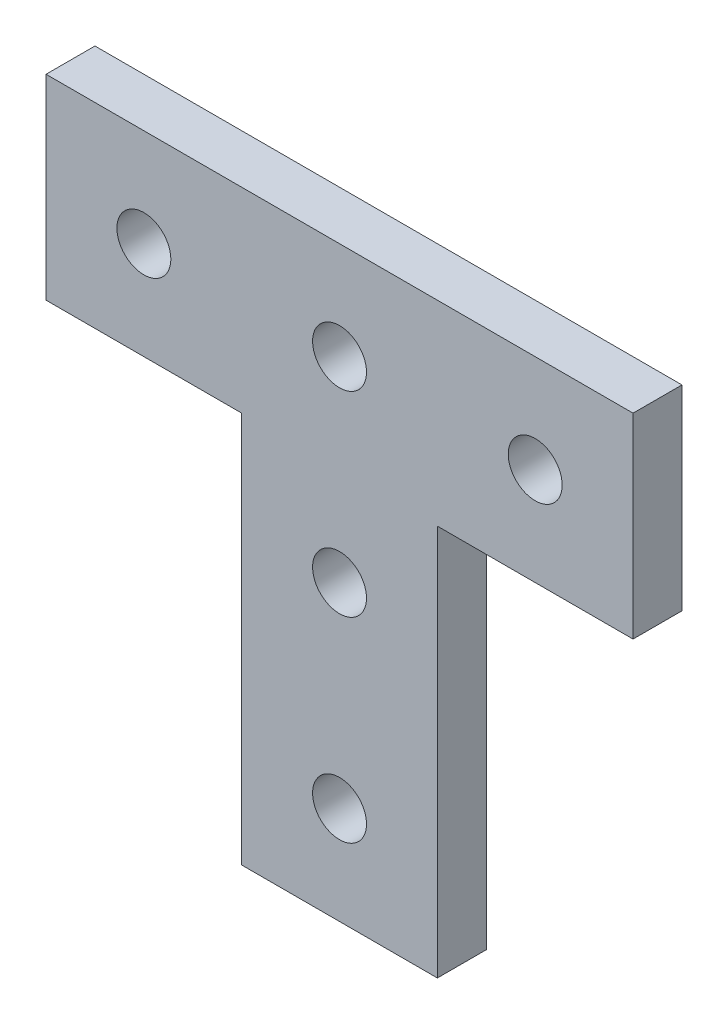
SolidWorks part; units mm, degrees
ref_plane "Front Plane" through (0, 0, 0) normal (0, 0, 1) x (1, 0, 0)
ref_plane "Top Plane" through (0, 0, 0) normal (0, 1, 0) x (1, 0, 0)
ref_plane "Right Plane" through (0, 0, 0) normal (1, 0, 0) x (0, 0, -1)
sketch "Sketch1" plane through (0, 0, 0) normal (0, 0, 1) x (1, 0, 0)
  line L0 (12.7, 0) -> (-12.7, 0)
  line L1 (-12.7, 0) -> (-12.7, 50.8)
  line L2 (-12.7, 50.8) -> (-38.1, 50.8)
  line L3 (-38.1, 50.8) -> (-38.1, 76.2)
  line L4 (-38.1, 76.2) -> (38.1, 76.2)
  line L5 (38.1, 76.2) -> (38.1, 50.8)
  line L6 (38.1, 50.8) -> (12.7, 50.8)
  line L7 (12.7, 50.8) -> (12.7, 0)
  dimension "D1" = 25.4
  dimension "D2" = 12.7
  dimension "D3" = 50.8
  dimension "D4" = 25.4
  dimension "D5" = 25.4
  dimension "D6" = 25.4
  dimension "D7" = 25.4
extrude "Boss-Extrude1" add sketch "Sketch1" along normal blind 6.35
sketch "Sketch2" plane through (0, 0, 6.35) normal (0, 0, 1) x (1, 0, 0)
  line L0 (0, 0) -> (0, 76.2) construction
  line L1 (38.1, 76.2) -> (-38.1, 76.2) construction
  line L2 (-38.1, 63.5) -> (38.1, 63.5) construction
  line L3 (-38.1, 76.2) -> (-38.1, 50.8) construction
  line L4 (38.1, 50.8) -> (38.1, 76.2) construction
  line L5 (-12.7, 0) -> (12.7, 0) construction
  circle A0 centre (0, 63.5) radius 3.5
  circle A1 centre (25.4, 63.5) radius 3.5
  circle A2 centre (-25.4, 63.5) radius 3.5
  circle A3 centre (0, 38.1) radius 3.5
  circle A4 centre (0, 12.7) radius 3.5
  dimension "D1" = 7
  dimension "D2" = 7
  dimension "D3" = 7
  dimension "D4" = 7
  dimension "D5" = 7
  dimension "D6" = 12.7
  dimension "D7" = 25.4
  dimension "D8" = 25.4
  dimension "D9" = 25.4
extrude "Cut-Extrude1" cut sketch "Sketch2" against normal through all
